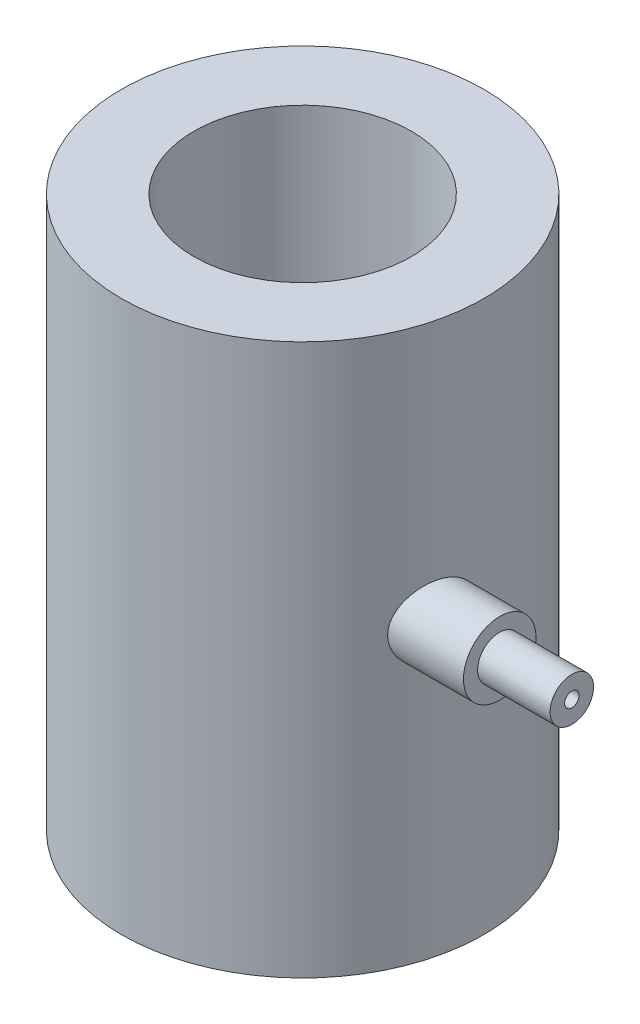
SolidWorks part; units mm, degrees
ref_plane "Alzado" through (0, 0, 0) normal (0, 0, 1) x (1, 0, 0)
ref_plane "Planta" through (0, 0, 0) normal (0, 1, 0) x (1, 0, 0)
ref_plane "Vista lateral" through (0, 0, 0) normal (1, 0, 0) x (0, 0, -1)
sketch "Croquis1" plane through (0, 0, 0) normal (0, 1, 0) x (1, 0, 0)
  circle A0 centre (0, 0) radius 12.5
  circle A1 centre (0, 0) radius 7.5
extrude "Saliente-Extruir1" add sketch "Croquis1" along normal blind 38
sketch "Croquis2" plane through (0, 0, 0) normal (1, 0, 0) x (0, 0, -1)
  circle A0 centre (-2.9057, 19.9651) radius 2.5
extrude "Saliente-Extruir2" add sketch "Croquis2" along normal blind 16.5
sketch "Croquis3" plane through (0, 38, 0) normal (0, 1, 0) x (1, 0, 0)
  circle A1 centre (0, 0) radius 7.5
extrude "Cortar-Extruir1" cut sketch "Croquis3" against normal blind 38
sketch "Croquis4" plane through (16.5, 0, 0) normal (1, 0, 0) x (0, 0, -1)
  circle A0 centre (-2.9334, 20.0215) radius 1.5
extrude "Saliente-Extruir7" add sketch "Croquis4" along normal blind 5
sketch "Croquis5" plane through (21.5, 0, 0) normal (1, 0, 0) x (0, 0, -1)
  circle A0 centre (-2.9334, 20.0215) radius 0.5
extrude "Cortar-Extruir2" cut sketch "Croquis5" against normal blind 22
scale "Escala1" scale about centroid uniform scaling yes scale factor 7
